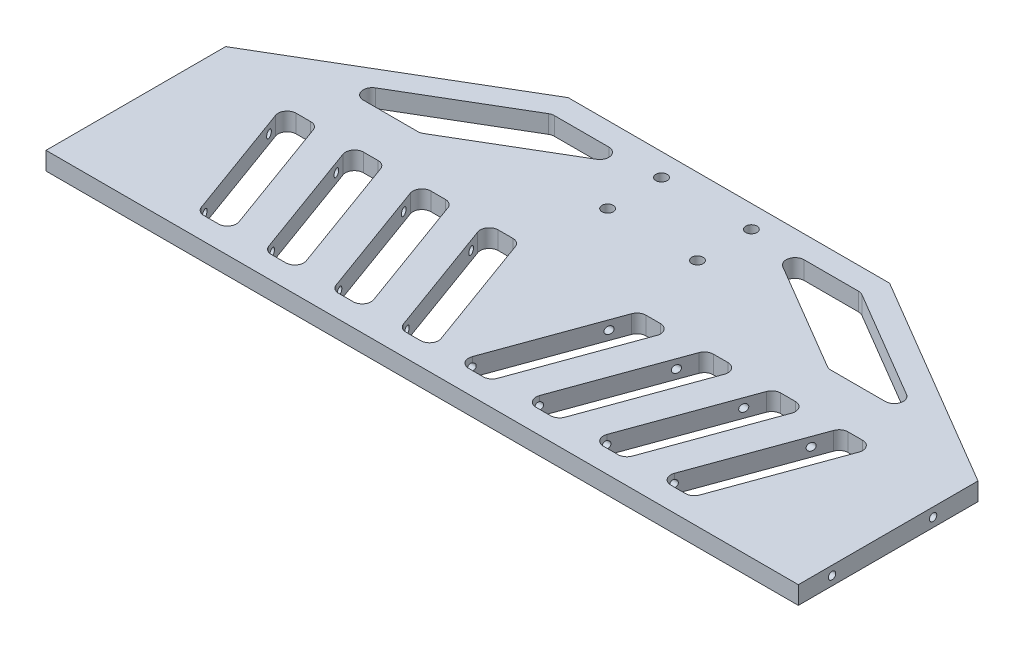
SolidWorks part; units mm, degrees
ref_plane "Ebene vorne" through (0, 0, 0) normal (0, 0, 1) x (1, 0, 0)
ref_plane "Ebene oben" through (0, 0, 0) normal (0, 1, 0) x (1, 0, 0)
ref_plane "Ebene rechts" through (0, 0, 0) normal (1, 0, 0) x (0, 0, -1)
sketch "Skizze3" plane through (0, 0, 0) normal (0, 1, 0) x (1, 0, 0)
  line L0 (0, 0) -> (0, 96.5783) construction
  line L1 (167.5, -40) -> (-167.5, -40)
  line L2 (167.5, -40) -> (167.5, 40)
  line L3 (-167.5, 40) -> (-71.5557, 96.5783)
  line L4 (-167.5, -40) -> (-167.5, 40)
  line L5 (167.5, -40) -> (-167.5, 40) construction
  line L6 (167.5, 40) -> (-167.5, -40) construction
  line L7 (-71.5557, 96.5783) -> (71.5557, 96.5783)
  line L8 (167.5, 40) -> (71.5557, 96.5783)
  circle A0 centre (-20, 86.5783) radius 2.5
  circle A1 centre (-20, 62.5783) radius 2.5
  circle A2 centre (20, 62.5783) radius 2.5
  circle A3 centre (20, 86.5783) radius 2.5
  point P0 (0, 0)
  dimension "D3" = 5
  dimension "D4" = 5
  dimension "D8" = 10
  dimension "D1" = 335
  dimension "D2" = 80
  dimension "D5" = 24
  dimension "D6" = 20
  dimension "D7" = 20
extrude "Aufsatz-Linear austragen2" add sketch "Skizze3" along normal blind 8
hole_wizard "M4 Gewindebohrung1" positions "Skizze4" profile "Skizze6" tap size "M4" standard "DIN" end condition through all
sketch "Skizze4" plane through (167.5, 0, 0) normal (1, 0, 0) x (0, 0, -1)
  line L0 (-40, 4) -> (40, 4) construction
  line L1 (-40, 8) -> (-40, 0) construction
  line L2 (40, 8) -> (40, 0) construction
  point P0 (-25, 4)
  point P2 (20, 4)
  dimension "D1" = 45
  dimension "D2" = 15
cosmetic thread "Bohrungsgewinde1" parameters "D2"=4
cosmetic thread "Bohrungsgewinde2" parameters "D2"=4
sketch "Skizze6" plane through (167.5, 4, 25) normal (0, 1, 0) x (0, 0, -1)
  line L0 (0, 0) -> (0, 335)
  line L1 (0, 335) -> (1.65, 335)
  line L2 (1.65, 335) -> (1.65, 0)
  line L5 (1.65, 0) -> (0, 0)
  line L11 (0, -6.35) -> (0, 107.95) construction
  dimension "Bohrerdurchmesser" = 3.3
  dimension "Bohrungstiefe" = 335
sketch "Skizze7" plane through (0, 8, 0) normal (0, 1, 0) x (1, 0, 0)
  line L0 (0, 96.5783) -> (0, -40) construction
  line L1 (71.5557, 96.5783) -> (-71.5557, 96.5783) construction
  line L2 (-167.5, -40) -> (167.5, -40) construction
  line L3 (-167.5, 40) -> (167.5, 40) construction
  line L4 (-36.1256, 30) -> (-29.639, 30)
  line L5 (-39.8844, 24.6319) -> (-20.9579, -27.3681)
  line L6 (-25.8803, 27.3681) -> (-6.9538, -24.6319)
  line L7 (-17.1992, -30) -> (-10.7126, -30)
  line L8 (-55.8803, 27.3681) -> (-36.9538, -24.6319)
  line L9 (-47.1992, -30) -> (-40.7126, -30)
  line L10 (-69.8844, 24.6319) -> (-50.9579, -27.3681)
  line L11 (-66.1256, 30) -> (-59.639, 30)
  line L12 (-85.8803, 27.3681) -> (-66.9538, -24.6319)
  line L13 (-77.1992, -30) -> (-70.7126, -30)
  line L14 (-99.8844, 24.6319) -> (-80.9579, -27.3681)
  line L15 (-96.1256, 30) -> (-89.639, 30)
  line L16 (-115.8803, 27.3681) -> (-96.9538, -24.6319)
  line L17 (-107.1992, -30) -> (-100.7126, -30)
  line L18 (-129.8844, 24.6319) -> (-110.9579, -27.3681)
  line L19 (-126.1256, 30) -> (-119.639, 30)
  line L20 (126.1256, 30) -> (119.639, 30)
  line L21 (129.8844, 24.6319) -> (110.9579, -27.3681)
  line L22 (107.1992, -30) -> (100.7126, -30)
  line L23 (115.8803, 27.3681) -> (96.9538, -24.6319)
  line L24 (96.1256, 30) -> (89.639, 30)
  line L25 (99.8844, 24.6319) -> (80.9579, -27.3681)
  line L26 (77.1992, -30) -> (70.7126, -30)
  line L27 (85.8803, 27.3681) -> (66.9538, -24.6319)
  line L28 (66.1256, 30) -> (59.639, 30)
  line L29 (69.8844, 24.6319) -> (50.9579, -27.3681)
  line L30 (47.1992, -30) -> (40.7126, -30)
  line L31 (55.8803, 27.3681) -> (36.9538, -24.6319)
  line L32 (17.1992, -30) -> (10.7126, -30)
  line L33 (25.8803, 27.3681) -> (6.9538, -24.6319)
  line L34 (39.8844, 24.6319) -> (20.9579, -27.3681)
  line L35 (36.1256, 30) -> (29.639, 30)
  arc A0 (-6.9538, -24.6319) -> (-10.7126, -30) centre (-10.7126, -26) cw
  arc A1 (-20.9579, -27.3681) -> (-17.1992, -30) centre (-17.1992, -26) ccw
  arc A2 (-29.639, 30) -> (-25.8803, 27.3681) centre (-29.639, 26) cw
  arc A3 (-39.8844, 24.6319) -> (-36.1256, 30) centre (-36.1256, 26) cw
  arc A4 (-77.1992, -30) -> (-80.9579, -27.3681) centre (-77.1992, -26) cw
  arc A5 (-107.1992, -30) -> (-110.9579, -27.3681) centre (-107.1992, -26) cw
  arc A6 (-96.9538, -24.6319) -> (-100.7126, -30) centre (-100.7126, -26) cw
  arc A7 (-66.9538, -24.6319) -> (-70.7126, -30) centre (-70.7126, -26) cw
  arc A8 (-36.9538, -24.6319) -> (-40.7126, -30) centre (-40.7126, -26) cw
  arc A9 (-55.8803, 27.3681) -> (-59.639, 30) centre (-59.639, 26) ccw
  arc A10 (-69.8844, 24.6319) -> (-66.1256, 30) centre (-66.1256, 26) cw
  arc A11 (-85.8803, 27.3681) -> (-89.639, 30) centre (-89.639, 26) ccw
  arc A12 (-99.8844, 24.6319) -> (-96.1256, 30) centre (-96.1256, 26) cw
  arc A13 (-115.8803, 27.3681) -> (-119.639, 30) centre (-119.639, 26) ccw
  arc A14 (-129.8844, 24.6319) -> (-126.1256, 30) centre (-126.1256, 26) cw
  arc A15 (-47.1992, -30) -> (-50.9579, -27.3681) centre (-47.1992, -26) cw
  arc A16 (47.1992, -30) -> (50.9579, -27.3681) centre (47.1992, -26) ccw
  arc A17 (129.8844, 24.6319) -> (126.1256, 30) centre (126.1256, 26) ccw
  arc A18 (115.8803, 27.3681) -> (119.639, 30) centre (119.639, 26) cw
  arc A19 (99.8844, 24.6319) -> (96.1256, 30) centre (96.1256, 26) ccw
  arc A20 (85.8803, 27.3681) -> (89.639, 30) centre (89.639, 26) cw
  arc A21 (69.8844, 24.6319) -> (66.1256, 30) centre (66.1256, 26) ccw
  arc A22 (55.8803, 27.3681) -> (59.639, 30) centre (59.639, 26) cw
  arc A23 (36.9538, -24.6319) -> (40.7126, -30) centre (40.7126, -26) ccw
  arc A24 (66.9538, -24.6319) -> (70.7126, -30) centre (70.7126, -26) ccw
  arc A25 (96.9538, -24.6319) -> (100.7126, -30) centre (100.7126, -26) ccw
  arc A26 (107.1992, -30) -> (110.9579, -27.3681) centre (107.1992, -26) ccw
  arc A27 (77.1992, -30) -> (80.9579, -27.3681) centre (77.1992, -26) ccw
  arc A28 (39.8844, 24.6319) -> (36.1256, 30) centre (36.1256, 26) ccw
  arc A29 (29.639, 30) -> (25.8803, 27.3681) centre (29.639, 26) ccw
  arc A30 (20.9579, -27.3681) -> (17.1992, -30) centre (17.1992, -26) cw
  arc A31 (6.9538, -24.6319) -> (10.7126, -30) centre (10.7126, -26) ccw
  point P28 (-5, -30)
  point P33 (-26.8382, 30)
  point P36 (-41.8382, 30)
  point P109 (41.8382, 30)
  point P110 (26.8382, 30)
  point P111 (5, -30)
  dimension "D7" = 4
  dimension "D8" = 4
  dimension "D1" = 15
  dimension "D2" = 110
  dimension "D3" = 10
  dimension "D4" = 10
  dimension "D5" = 10
  dimension "D6" = 4
extrude "Schnitt-Linear austragen1" cut sketch "Skizze7" against normal blind 8
sketch "Skizze8" plane through (0, 8, 0) normal (0, 1, 0) x (1, 0, 0)
  line L0 (-118.2295, 57.4455) -> (-69.767, 86.0238)
  line L1 (-116.1977, 50) -> (-91.9471, 50)
  line L2 (-67.7352, 86.5783) -> (-43.4846, 86.5783)
  line L3 (-89.9152, 50.5545) -> (-41.4528, 79.1328)
  line L5 (71.5557, 96.5783) -> (-71.5557, 96.5783) construction
  line L7 (-71.5557, 96.5783) -> (-167.5, 40) construction
  line L8 (0, 96.5783) -> (0, 0) construction
  line L9 (89.9152, 50.5545) -> (41.4528, 79.1328)
  line L10 (67.7352, 86.5783) -> (43.4846, 86.5783)
  line L11 (116.1977, 50) -> (91.9471, 50)
  line L12 (118.2295, 57.4455) -> (69.767, 86.0238)
  arc A0 (-91.9471, 50) -> (-89.9152, 50.5545) centre (-91.9471, 54) ccw
  arc A1 (-43.4846, 86.5783) -> (-41.4528, 79.1328) centre (-43.4846, 82.5783) cw
  arc A2 (-69.767, 86.0238) -> (-67.7352, 86.5783) centre (-67.7352, 82.5783) cw
  arc A3 (-116.1977, 50) -> (-118.2295, 57.4455) centre (-116.1977, 54) cw
  arc A4 (116.1977, 50) -> (118.2295, 57.4455) centre (116.1977, 54) ccw
  arc A5 (69.767, 86.0238) -> (67.7352, 86.5783) centre (67.7352, 82.5783) ccw
  arc A6 (43.4846, 86.5783) -> (41.4528, 79.1328) centre (43.4846, 82.5783) ccw
  arc A7 (91.9471, 50) -> (89.9152, 50.5545) centre (91.9471, 54) cw
  point P11 (-90.8555, 50)
  point P18 (-130.8555, 50)
  point P34 (130.8555, 50)
  point P35 (90.8555, 50)
  dimension "D5" = 4
  dimension "D1" = 10
  dimension "D2" = 10
  dimension "D3" = 10
  dimension "D4" = 40
extrude "Schnitt-Linear austragen2" cut sketch "Skizze8" against normal blind 8
